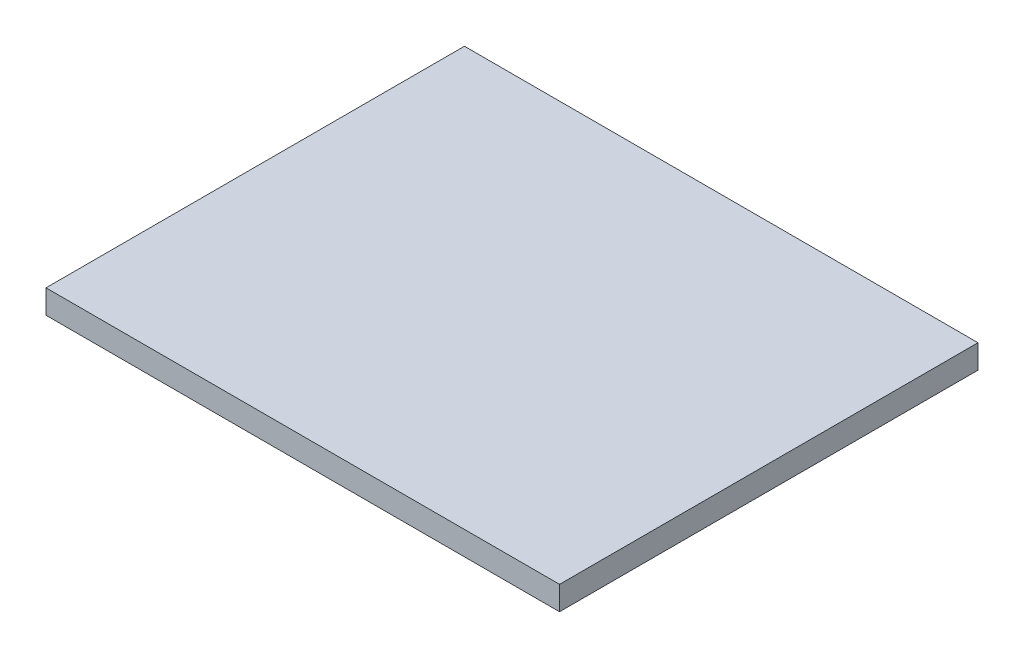
SolidWorks part; units mm, degrees
ref_plane "Front Plane" through (0, 0, 0) normal (0, 0, 1) x (1, 0, 0)
ref_plane "Top Plane" through (0, 0, 0) normal (0, 1, 0) x (1, 0, 0)
ref_plane "Right Plane" through (0, 0, 0) normal (1, 0, 0) x (0, 0, -1)
sketch "Sketch1" plane through (0, 0, 0) normal (0, 0, 1) x (1, 0, 0)
  line L0 (64.8, -100) -> (0, -100)
  line L1 (64.8, -100) -> (64.8, -103)
  line L2 (0, -100) -> (0, -103)
  line L3 (64.8, -103) -> (0, -103)
  line L6 (0, 25) -> (0, -100) construction
  line L8 (0, -100) -> (249.6, -100) construction
  line L9 (64.8, -350.4) -> (64.8, 0) construction
  dimension "D1" = 3
extrude "Boss-Extrude1" add sketch "Sketch1" along normal up to surface (52.8 mm away)
